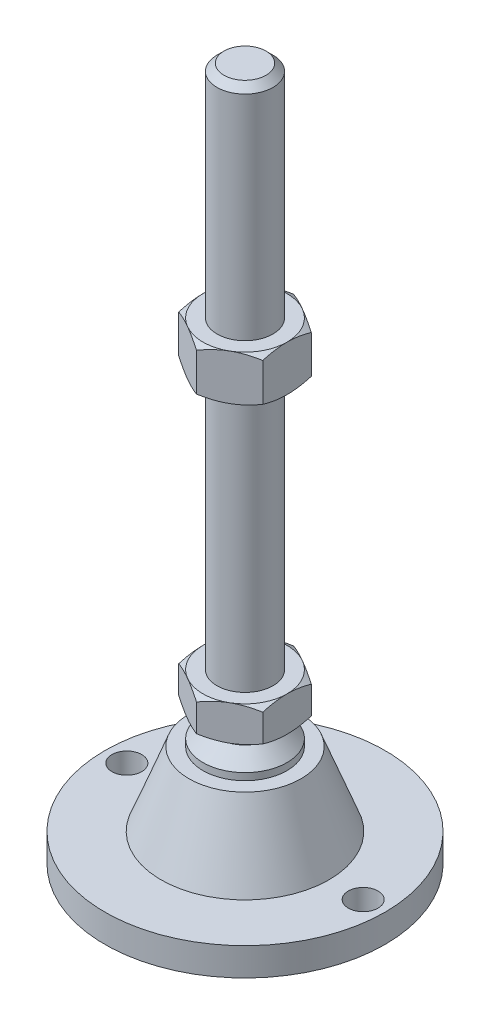
SolidWorks part; units mm, degrees
ref_plane "Спереди" through (0, 0, 0) normal (0, 0, 1) x (1, 0, 0)
ref_plane "Сверху" through (0, 0, 0) normal (0, 1, 0) x (1, 0, 0)
ref_plane "Справа" through (0, 0, 0) normal (1, 0, 0) x (0, 0, -1)
sketch "Эскиз1" plane through (0, 0, 0) normal (0, 0, 1) x (1, 0, 0)
  line L0 (0, 0) -> (-40, 0)
  line L3 (-40, 0) -> (-40, 8)
  line L12 (-8, 48) -> (-8, 196)
  line L13 (-8, 196) -> (-6, 198)
  line L14 (-6, 198) -> (0, 198)
  line L15 (0, 198) -> (0, 0) construction
  line L16 (-40, 8) -> (-24, 8)
  line L17 (0, 0) -> (0, 198)
  line L18 (0, 0) -> (0, -7.9595) construction
  line L19 (-8, 48) -> (-8, 38)
  line L21 (-12, 29) -> (-16, 29)
  line L22 (-24, 8) -> (-16, 29)
  line L23 (-12, 29) -> (-12, 31)
  line L24 (-12, 31) -> (-8, 35)
  line L25 (-8, 35) -> (-8, 38)
  line L26 (-8, 48) -> (0, 48) construction
  point P8 (-8, 122)
revolve "Повернуть1" add sketch "Эскиз1" angle 360 about L17
ref_plane "Плоскость2" through (0, 38, 0) normal (0, 1, 0) x (1, 0, 0)
sketch "Эскиз2" plane through (0, 38, 0) normal (0, 1, 0) x (1, 0, 0)
  line L1 (0, 13.8564) -> (-12, 6.9282)
  line L2 (-12, 6.9282) -> (-12, -6.9282)
  line L3 (-12, -6.9282) -> (0, -13.8564)
  line L4 (0, -13.8564) -> (12, -6.9282)
  line L5 (12, -6.9282) -> (12, 6.9282)
  line L6 (12, 6.9282) -> (0, 13.8564)
  circle A0 centre (0, 0) radius 12 construction
  dimension "D1" = 24
extrude "Бобышка-Вытянуть1" add sketch "Эскиз2" along normal up to vertex (10 mm away) up to point (-8, 48, 0)
ref_plane "Плоскость1" through (0, 122, 0) normal (0, 1, 0) x (1, 0, 0)
sketch "Эскиз3" plane through (0, 122, 0) normal (0, 1, 0) x (1, 0, 0)
  line L6 (12, 6.9282) -> (0, 13.8564)
  line L7 (0, 13.8564) -> (-12, 6.9282)
  line L8 (-12, 6.9282) -> (-12, -6.9282)
  line L9 (-12, -6.9282) -> (0, -13.8564)
  line L10 (0, -13.8564) -> (12, -6.9282)
  line L11 (12, -6.9282) -> (12, 6.9282)
  line L12 (12, 6.9282) -> (0, 13.8564)
  line L13 (0, 13.8564) -> (-12, 6.9282)
  line L14 (-12, 6.9282) -> (-12, -6.9282)
  line L15 (-12, -6.9282) -> (0, -13.8564)
  line L16 (0, -13.8564) -> (12, -6.9282)
  line L17 (12, -6.9282) -> (12, 6.9282)
  dimension "D1" = 0
extrude "Бобышка-Вытянуть2" add sketch "Эскиз3" along normal blind 13
sketch "Эскиз4" plane through (0, 0, 0) normal (0, 0, 1) x (1, 0, 0)
  line L0 (-12, 135) -> (-23.2583, 128.5)
  line L1 (-23.2583, 128.5) -> (-23.2583, 135)
  line L2 (-23.2583, 135) -> (-12, 135)
  line L3 (-23.2583, 128.5) -> (-12, 122)
  line L4 (50, 122) -> (-50, 122) construction
  line L5 (-12, 122) -> (-23.2583, 122)
  line L6 (-23.2583, 122) -> (-23.2583, 128.5)
  line L7 (-12, 135) -> (-12, 122) construction
  line L8 (-12, 48) -> (-20.6603, 48)
  line L9 (-20.6603, 48) -> (-20.6603, 43)
  line L10 (-20.6603, 43) -> (-12, 48)
  line L11 (-12, 38) -> (-20.6603, 43)
  line L12 (-20.6603, 43) -> (-20.6603, 38)
  line L13 (-20.6603, 38) -> (-12, 38)
  line L14 (0, 198) -> (0, 96.3793) construction
  line L15 (50, 38) -> (-50, 38) construction
  dimension "D1" = 30
  dimension "D2" = 30
revolve "Вырез-Повернуть2" cut sketch "Эскиз4" angle 360 about L14
sketch "Эскиз5" plane through (0, 8, 0) normal (0, 1, 0) x (1, 0, 0)
  line L0 (33.75, 0) -> (-33.75, 0) construction
  circle A0 centre (-33.75, 0) radius 4.25
  circle A1 centre (33.75, 0) radius 4.25
  circle A2 centre (0, 0) radius 40 construction
  dimension "D1" = 8.5
  dimension "D2" = 2
extrude "Вырез-Вытянуть1" cut sketch "Эскиз5" against normal through all
equation "\"D13@Эскиз1\"=\"D12@Эскиз1\"/2"
